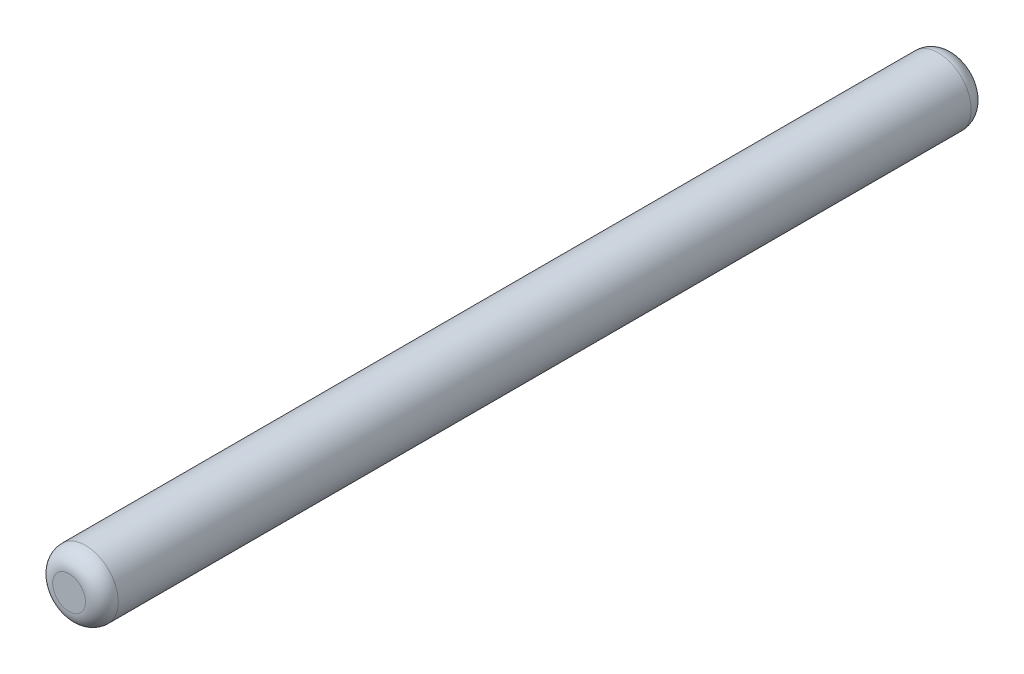
SolidWorks part; units mm, degrees
ref_plane "Front" through (0, 0, 0) normal (0, 0, 1) x (1, 0, 0)
ref_plane "Top" through (0, 0, 0) normal (0, 1, 0) x (1, 0, 0)
ref_plane "Right" through (0, 0, 0) normal (1, 0, 0) x (0, 0, -1)
sketch "Sketch1" plane through (0, 0, 0) normal (0, 0, 1) x (1, 0, 0)
  circle A0 centre (0, 0) radius 2
  dimension "D1" = 4
extrude "Boss-Extrude1" add sketch "Sketch1" along normal mid plane 54
fillet "Fillet1" radius 1 1 edges at (2, 0, 27)
fillet "Fillet2" radius 1 1 edges at (2, 0, -27)
